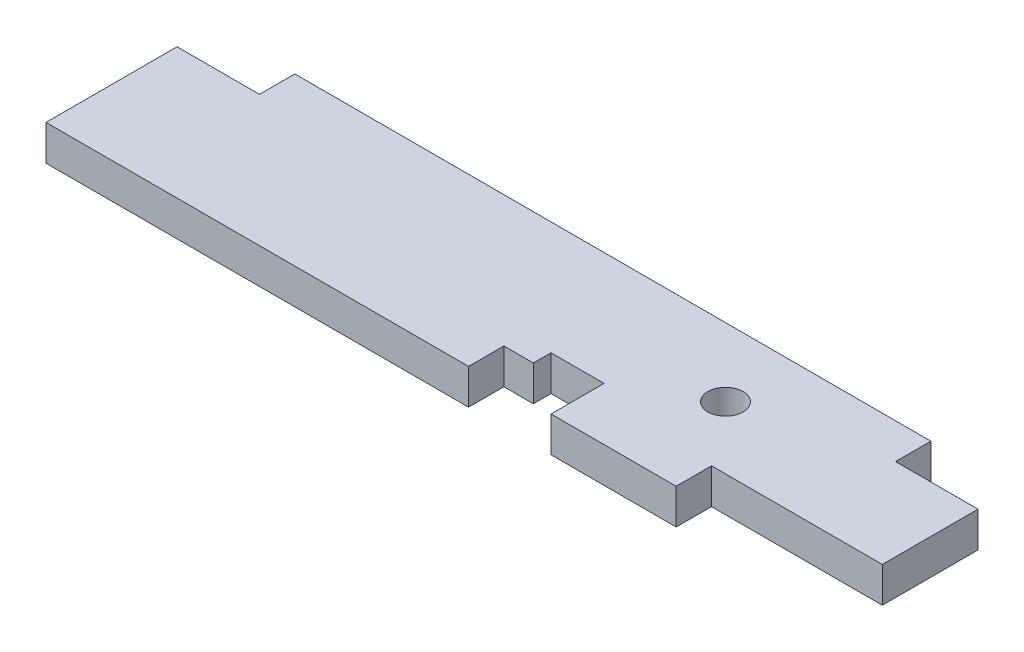
SolidWorks part; units mm, degrees
material "Pine"
ref_plane "Front Plane" through (0, 0, 0) normal (0, 0, 1) x (1, 0, 0)
ref_plane "Top Plane" through (0, 0, 0) normal (0, 1, 0) x (1, 0, 0)
ref_plane "Right Plane" through (0, 0, 0) normal (1, 0, 0) x (0, 0, -1)
sketch "Sketch1" plane through (0, 0, 0) normal (0, 1, 0) x (1, 0, 0)
  line L1 (0, 0) -> (774.7, 0)
  line L2 (0, 0) -> (0, -179.3875)
  line L3 (0, -179.3875) -> (863.6, -179.3875)
  line L4 (863.6, -38.1) -> (863.6, -179.3875)
  line L6 (774.7, 0) -> (774.7, -38.1)
  line L7 (774.7, -38.1) -> (863.6, -38.1)
  circle A0 centre (627.126, -73.914) radius 19.05
  dimension "D7" = 38.1
  dimension "D1" = 179.3875
  dimension "D2" = 774.7
  dimension "D3" = 863.6
  dimension "D4" = 38.1
  dimension "D5" = 627.126
  dimension "D6" = 73.914
extrude "Boss-Extrude1" add sketch "Sketch1" along normal blind 38.1
sketch "Sketch7" plane through (0, 38.1, 0) normal (0, 1, 0) x (1, 0, 0)
  line L8 (455.6125, -141.2875) -> (487.3625, -141.2875)
  line L9 (455.6125, -141.2875) -> (455.6125, -179.3875)
  line L10 (455.6125, -179.3875) -> (544.5125, -179.3875)
  line L12 (774.7, 0) -> (0, 0) construction
  line L13 (0, -179.3875) -> (863.6, -179.3875) construction
  line L18 (544.5125, -179.3875) -> (544.5125, -122.2375)
  line L19 (544.5125, -122.2375) -> (487.3625, -122.2375)
  line L20 (487.3625, -141.2875) -> (487.3625, -122.2375)
  dimension "D1" = 141.2875
  dimension "D2" = 455.6125
  dimension "D3" = 88.9
  dimension "D4" = 487.3625
  dimension "D5" = 122.2375
extrude "Cut-Extrude5" cut sketch "Sketch7" against normal through all
sketch "Sketch8" plane through (0, 38.1, 0) normal (0, 1, 0) x (1, 0, 0)
  line L1 (679.45, -179.3875) -> (863.6, -179.3875)
  line L2 (679.45, -179.3875) -> (679.45, -141.2748)
  line L3 (679.45, -141.2748) -> (863.6, -141.2748)
  line L4 (863.6, -179.3875) -> (863.6, -141.2748)
  line L5 (863.6, -179.3875) -> (863.6, -38.1) construction
  line L6 (0, -179.3875) -> (455.6125, -179.3875) construction
  dimension "D1" = 141.2748
  dimension "D2" = 679.45
extrude "Cut-Extrude6" cut sketch "Sketch8" against normal through all
sketch "Sketch9" plane through (0, 0, 0) normal (0, -1, 0) x (1, 0, 0)
  line L1 (0, 0) -> (88.9, 0)
  line L2 (0, 0) -> (0, 38.1)
  line L3 (0, 38.1) -> (88.9, 38.1)
  line L4 (88.9, 0) -> (88.9, 38.1)
  dimension "D1" = 88.9
  dimension "D2" = 38.1
extrude "Cut-Extrude7" cut sketch "Sketch9" against normal through all
